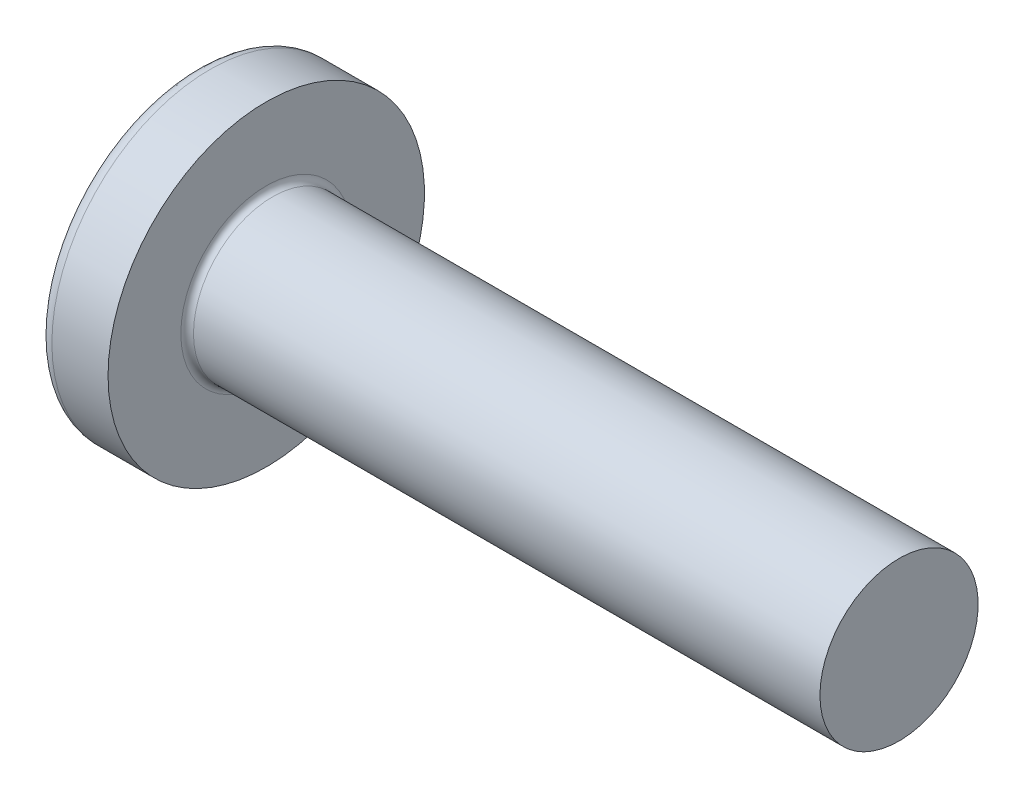
SolidWorks part; units mm, degrees
ref_plane "Plane1" through (0, 0, 0) normal (0, 0, 1) x (1, 0, 0)
ref_plane "Plane2" through (0, 0, 0) normal (0, 1, 0) x (1, 0, 0)
ref_plane "Plane3" through (0, 0, 0) normal (1, 0, 0) x (0, 0, -1)
sketch "BodySke" plane through (0, 0, 0) normal (0, 0, 1) x (1, 0, 0)
  line L0 (7.5, 5) -> (7.5, 10)
  line L1 (8.25, 6.35) -> (8.25, -3.175) construction
  line L2 (-25.4, 0) -> (127, 0) construction
  line L3 (47.5, 0) -> (0, 0)
  line L4 (7.5, 5) -> (47.5, 5)
  line L5 (47.5, 5) -> (47.5, 0)
  line L6 (3.9501, 10) -> (7.5, 10)
  line L8 (7.5, 6.35) -> (7.5, -3.175) construction
  arc A0 (3.2319, 9.6424) -> (0, 0) centre (16, 0) ccw
  arc A2 (3.2319, 9.6424) -> (3.9501, 10) centre (3.9501, 9.1) cw
revolve "Base-Revolve" add sketch "BodySke"
cosmetic thread "ThreadCosmetic" [suppressed]
fillet "Fillet1" radius 0.4 1 edges at (7.5, 0, 5)
sketch "Sketch3" plane through (0, 0, 0) normal (1, 0, 0) x (0, 0, -1)
  line L0 (1.08, -4.95) -> (-1.08, -4.95)
  line L1 (1.08, -4.95) -> (1.08, 4.95)
  line L2 (-1.08, 4.95) -> (1.08, 4.95)
  line L3 (-1.08, 4.95) -> (-1.08, -4.95)
  dimension "D1" = 1.3
  dimension "D2" = 0.37
ref_plane "Plane4" through (5.69, 0, 0) normal (1, 0, 0) x (0, 0, -1)
sketch "Sketch4" plane through (5.69, 0, 0) normal (1, 0, 0) x (0, 0, -1)
  line L0 (1.08, -2.1131) -> (-1.08, -2.1131)
  line L1 (1.08, -2.1131) -> (1.08, 2.1131)
  line L2 (-1.08, 2.1131) -> (1.08, 2.1131)
  line L3 (-1.08, 2.1131) -> (-1.08, -2.1131)
  dimension "D1" = 0.74
  dimension "D2" = 1.1043
  dimension "D3" = 0.37
  dimension "D4" = 0.5521
loft "Recess" cut profiles "Sketch3", "Sketch4"
pattern_circular "RecPat" count 2 every 90 about axis through (0, 0, 0) along (1, 0, 0) of "Recess"
sketch "RecCorSke" plane through (0, 0, 0) normal (0, 0, 1) x (1, 0, 0)
  line L0 (-3.175, 0) -> (15.875, 0) construction
  line L1 (-25.4, 0) -> (127, 0) construction
  line L2 (0, 0) -> (0, 2.3284)
  line L3 (0, 2.3284) -> (5.69, 1.9305)
  line L4 (5.69, 1.9305) -> (6.3173, 0)
  line L5 (6.3173, 0) -> (0, 0)
  dimension "Depth" = 1.5
  dimension "Draft_angle" = 4
  dimension "Bottom_angle" = 18
revolve "RecessCore" cut sketch "RecCorSke" angle 360 about L0
sketch "ThdSchSke" plane through (0, 0, 0) normal (0, 0, 1) x (1, 0, 0)
  line L0 (10.5, -4.172) -> (9.9202, -5)
  line L1 (10.5, -4.172) -> (11.0798, -5)
  line L2 (11.0798, -5) -> (11.0798, -6.25)
  line L3 (-3.175, 0) -> (5.1513, 0) construction
  line L5 (11.0798, -6.25) -> (9.9202, -6.25)
  line L6 (9.9202, -6.25) -> (9.9202, -5)
  dimension "SideAngle" = 55
  dimension "VeeAngle" = 70
  dimension "Thread_minor" = 1.993
  dimension "Overcut" = 3.125
  dimension "Diameter" = 2.5
  dimension "Start" = 3
revolve "ThreadSchematic" [suppressed] cut sketch "ThdSchSke" angle 360 about L3
pattern_linear "ThdSchPat" [suppressed]
equation "\"D1@Sketch3\" = \"Cross_dia@Sketch3\" / 2"
equation "\"D2@Sketch3\" = \"Cross_width@Sketch3\" / 2"
equation "\"Depth@RecCorSke\" = \"Cross_depth@Plane4\""
equation "\"D1@Sketch4\" = \"Cross_width@Sketch3\""
equation "\"D2@Sketch4\" = \"Cross_dia@Sketch3\" - 2.0 * \"Cross_depth@Plane4\" * tan(26.5  * 0.017453292)"
equation "\"D3@Sketch4\" = \"D1@Sketch4\" / 2"
equation "\"D4@Sketch4\" = \"D2@Sketch4\" / 2"
equation "\"Thread_length@ThreadCosmetic\" = ((sgn( (\"Length@BodySke\" - \"Advance@BodySke\" * 2.0 ) - \"Thread_nom@BodySke\" )-1)*( (\"Length@BodySke\" - \"Advance@BodySke\" * 2.0 ) - \"Thread_nom@BodySke\" ))/-2+ \"Thread_nom@BodySke\""
equation "\"Thread_minor@ThdSchSke\" = \"Thread_minor@ThreadCosmetic\""
equation "\"Diameter@ThdSchSke\" = \"Diameter@BodySke\""
equation "\"Overcut@ThdSchSke\" = \"Diameter@BodySke\" * 1.25"
equation "\"Start@ThdSchSke\" = \"Head_ht@BodySke\" + \"Length@BodySke\" - \"Thread_length@ThreadCosmetic\"  '---Non-countersunk---"
equation "\"Num_threads@ThdSchPat\" = int( \"Thread_length@ThreadCosmetic\" / \"Advance@BodySke\" + 0.999 )  + 1"
equation "\"Advance@ThdSchPat\" = \"Thread_length@ThreadCosmetic\" /  (\"Num_threads@ThdSchPat\" - 1) 'relax it"
